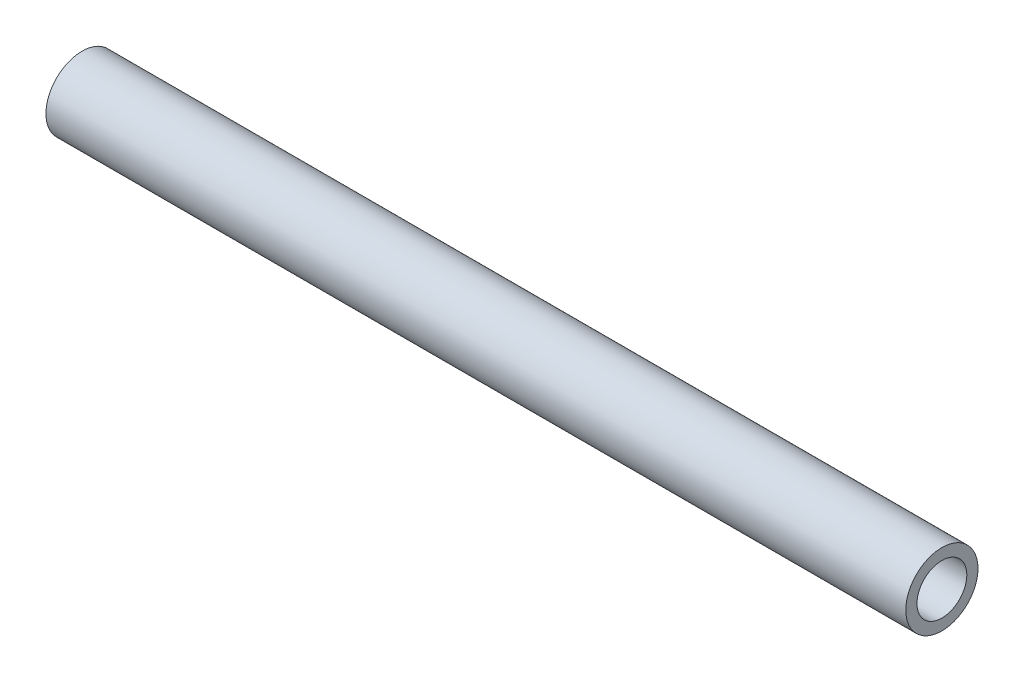
SolidWorks part; units mm, degrees
material "PVC 0.007 Plasticized"
ref_plane "Front Plane" through (0, 0, 0) normal (0, 0, 1) x (1, 0, 0)
ref_plane "Top Plane" through (0, 0, 0) normal (0, 1, 0) x (1, 0, 0)
ref_plane "Right Plane" through (0, 0, 0) normal (1, 0, 0) x (0, 0, -1)
sketch "Sketch1" plane through (0, 0, 0) normal (1, 0, 0) x (0, 0, -1)
  circle A0 centre (0, 0) radius 10.668
  circle A1 centre (0, 0) radius 7.366
  dimension "D1" = 21.336
  dimension "D2" = 14.732
extrude "Boss-Extrude1" add sketch "Sketch1" against normal blind 254
